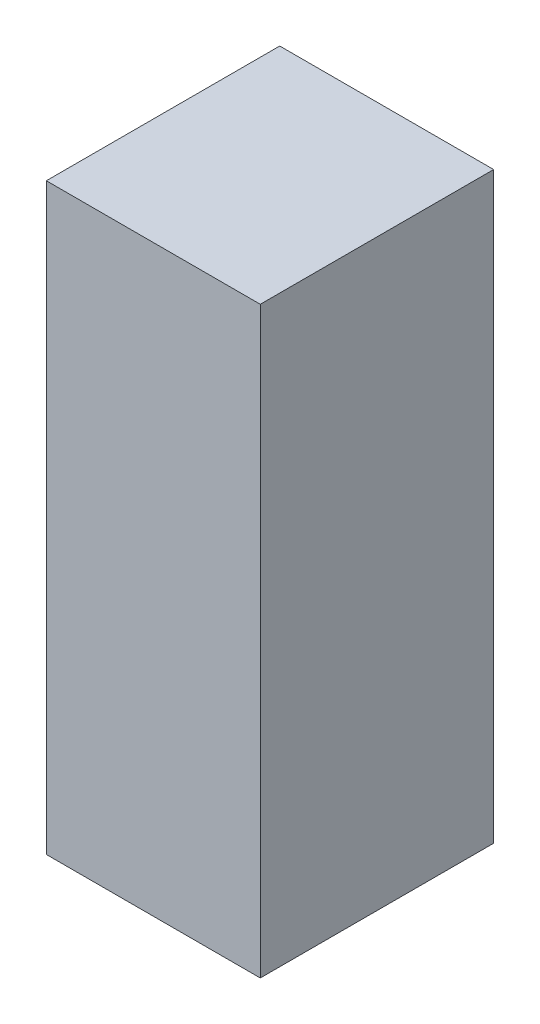
SolidWorks part; units mm, degrees
ref_plane "Front Plane" through (0, 0, 0) normal (0, 0, 1) x (1, 0, 0)
ref_plane "Top Plane" through (0, 0, 0) normal (0, 1, 0) x (1, 0, 0)
ref_plane "Right Plane" through (0, 0, 0) normal (1, 0, 0) x (0, 0, -1)
sketch "Sketch1" plane through (0, 0, 0) normal (0, 1, 0) x (1, 0, 0)
  line L1 (279.4, -304.8) -> (-279.4, -304.8)
  line L2 (279.4, -304.8) -> (279.4, 304.8)
  line L3 (279.4, 304.8) -> (-279.4, 304.8)
  line L4 (-279.4, -304.8) -> (-279.4, 304.8)
  line L5 (279.4, -304.8) -> (-279.4, 304.8) construction
  line L6 (279.4, 304.8) -> (-279.4, -304.8) construction
  point P0 (0, 0)
  dimension "D1" = 558.8
  dimension "D2" = 609.6
extrude "Boss-Extrude1" add sketch "Sketch1" along normal blind 1524
